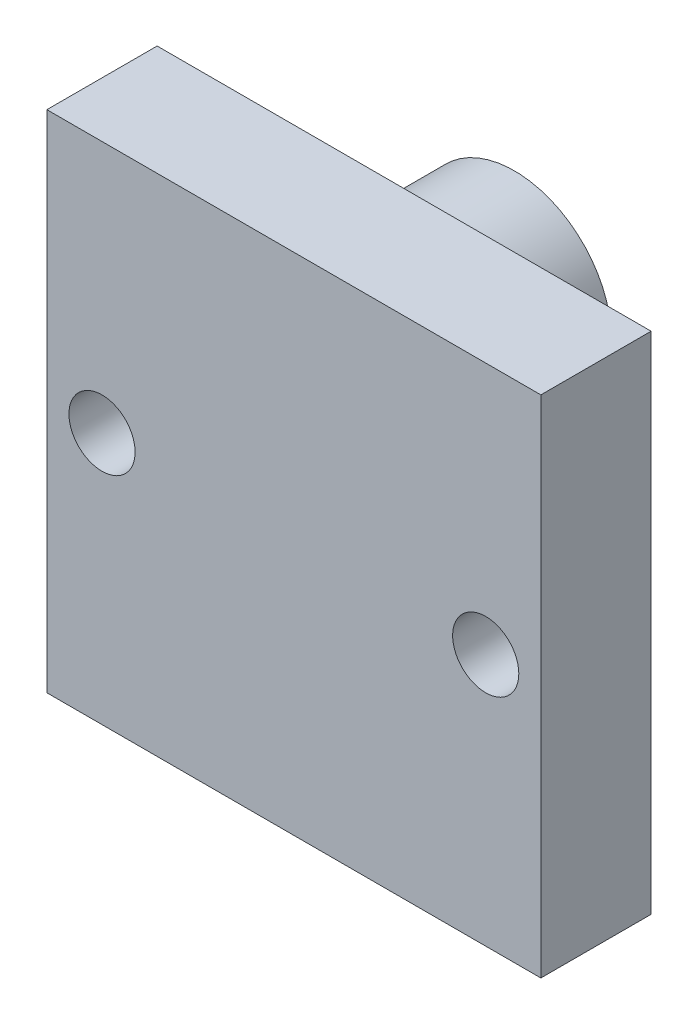
SolidWorks part; units mm, degrees
ref_plane "Front Plane" through (0, 0, 0) normal (0, 0, 1) x (1, 0, 0)
ref_plane "Top Plane" through (0, 0, 0) normal (0, 1, 0) x (1, 0, 0)
ref_plane "Right Plane" through (0, 0, 0) normal (1, 0, 0) x (0, 0, -1)
sketch "Sketch1" plane through (0, 0, 0) normal (0, 0, 1) x (1, 0, 0)
  line L1 (-11.2, 11.45) -> (11.2, 11.45)
  line L2 (-11.2, 11.45) -> (-11.2, -11.45)
  line L3 (-11.2, -11.45) -> (11.2, -11.45)
  line L4 (11.2, 11.45) -> (11.2, -11.45)
  line L5 (-11.2, 11.45) -> (11.2, -11.45) construction
  line L6 (-11.2, -11.45) -> (11.2, 11.45) construction
  point P0 (0, 0)
  dimension "D1" = 22.4
  dimension "D2" = 22.9
extrude "Boss-Extrude1" add sketch "Sketch1" along normal blind 5
sketch "Sketch2" plane through (0, 0, 5) normal (0, 0, 1) x (1, 0, 0)
  line L0 (0, 0) -> (-11.2, 0) construction
  line L1 (-11.2, 11.45) -> (-11.2, -11.45) construction
  line L2 (0, 0) -> (11.2, 0) construction
  line L3 (11.2, -11.45) -> (11.2, 11.45) construction
  line L4 (-11.2, 11.45) -> (-8.7, 11.45) construction
  line L5 (11.2, 11.45) -> (-11.2, 11.45) construction
  line L6 (11.2, 11.45) -> (8.7, 11.45) construction
  line L7 (-8.7, 11.45) -> (-8.7, 0) construction
  line L8 (8.7, 11.45) -> (8.7, 0) construction
  circle A0 centre (-8.7, 0) radius 1.5
  circle A1 centre (8.7, 0) radius 1.5
  dimension "D1" = 2.5
  dimension "D2" = 2.5
extrude "Cut-Extrude1" cut sketch "Sketch2" against normal blind 5
sketch "Sketch4" plane through (0, 0, 0) normal (0, 0, -1) x (-1, 0, 0)
  line L0 (-11.2, 11.45) -> (11.2, 11.45) construction
  line L1 (-11.2, 11.45) -> (11.2, 11.45) construction
  line L2 (0, 11.45) -> (0, 5.25) construction
  circle A0 centre (0, 5.25) radius 4.4
  dimension "D1" = 6.2
extrude "Boss-Extrude3" add sketch "Sketch4" along normal blind 5 contours A0
